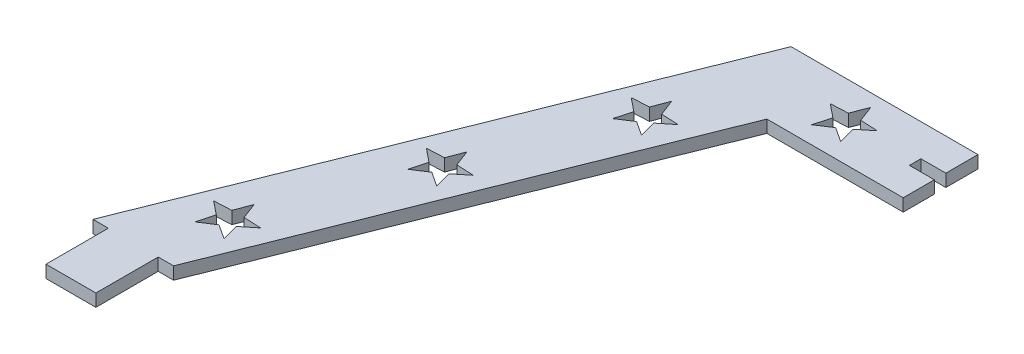
SolidWorks part; units mm, degrees
ref_plane "Front Plane" through (0, 0, 0) normal (0, 0, 1) x (1, 0, 0)
ref_plane "Top Plane" through (0, 0, 0) normal (0, 1, 0) x (1, 0, 0)
ref_plane "Right Plane" through (0, 0, 0) normal (1, 0, 0) x (0, 0, -1)
sketch "Sketch1" plane through (0, 0, 0) normal (0, 1, 0) x (1, 0, 0)
  line L0 (0, 0) -> (101.6, 0) construction
  line L1 (0, 0) -> (0, 127) construction
  line L2 (0, 127) -> (98.425, 127) construction
  line L3 (98.425, 127) -> (98.425, 118.8085)
  line L4 (98.425, 127) -> (50.8, 127)
  line L5 (50.8, 127) -> (0, 0)
  line L6 (0, 0) -> (3.9065, 0)
  line L7 (20.5175, 0) -> (63.6975, 107.95)
  line L8 (63.6975, 107.95) -> (98.425, 107.95)
  line L9 (3.9065, 0) -> (3.9065, -15.875)
  line L10 (3.9065, -15.875) -> (16.611, -15.875)
  line L11 (16.611, -15.875) -> (16.611, 0)
  line L12 (16.611, 0) -> (20.5175, 0)
  line L13 (98.425, 118.8085) -> (92.075, 118.8085)
  line L14 (92.075, 118.8085) -> (92.075, 115.8875)
  line L15 (92.075, 115.8875) -> (98.425, 115.8875)
  line L16 (98.425, 115.8875) -> (98.425, 107.95)
  line L17 (74.3563, 123.7542) -> (72.7878, 119.6338)
  line L18 (92.075, 117.348) -> (45.1512, 117.348) construction
  line L19 (50.8, 127) -> (63.6975, 107.95) construction
  line L20 (61.4274, 102.2747) -> (61.7931, 101.8616) construction
  line L21 (0, 0) -> (20.5175, 0) construction
  line L22 (10.2587, 0) -> (57.2487, 117.475) construction
  line L23 (80.3282, 119.4154) -> (75.9248, 119.6338)
  line L24 (74.3563, 123.7542) -> (75.9248, 119.6338)
  line L25 (80.3282, 119.4154) -> (76.8941, 116.6504)
  line L26 (78.0471, 112.395) -> (76.8941, 116.6504)
  line L27 (78.0471, 112.395) -> (74.3563, 114.8066)
  line L28 (70.6655, 112.395) -> (74.3563, 114.8066)
  line L29 (70.6655, 112.395) -> (71.8185, 116.6504)
  line L30 (68.3844, 119.4154) -> (71.8185, 116.6504)
  line L31 (68.3844, 119.4154) -> (72.7878, 119.6338)
  line L32 (47.6498, 99.7569) -> (46.0814, 95.6365)
  line L33 (53.6217, 95.4181) -> (49.2183, 95.6365)
  line L34 (47.6498, 99.7569) -> (49.2183, 95.6365)
  line L35 (53.6217, 95.4181) -> (50.1877, 92.6531)
  line L36 (51.3407, 88.3977) -> (50.1877, 92.6531)
  line L37 (51.3407, 88.3977) -> (47.6498, 90.8093)
  line L38 (43.959, 88.3977) -> (47.6498, 90.8093)
  line L39 (43.959, 88.3977) -> (45.112, 92.6531)
  line L40 (41.6779, 95.4181) -> (45.112, 92.6531)
  line L41 (41.6779, 95.4181) -> (46.0814, 95.6365)
  line L42 (32.7427, 62.489) -> (31.1742, 58.3686)
  line L43 (38.7146, 58.1502) -> (34.3111, 58.3686)
  line L44 (32.7427, 62.489) -> (34.3111, 58.3686)
  line L45 (38.7146, 58.1502) -> (35.2805, 55.3852)
  line L46 (36.4335, 51.1298) -> (35.2805, 55.3852)
  line L47 (36.4335, 51.1298) -> (32.7427, 53.5413)
  line L48 (29.0518, 51.1298) -> (32.7427, 53.5413)
  line L49 (29.0518, 51.1298) -> (30.2048, 55.3852)
  line L50 (26.7708, 58.1502) -> (30.2048, 55.3852)
  line L51 (26.7708, 58.1502) -> (31.1742, 58.3686)
  line L52 (17.2614, 23.7859) -> (15.693, 19.6655)
  line L53 (23.2333, 19.4471) -> (18.8299, 19.6655)
  line L54 (17.2614, 23.7859) -> (18.8299, 19.6655)
  line L55 (23.2333, 19.4471) -> (19.7993, 16.6821)
  line L56 (20.9523, 12.4267) -> (19.7993, 16.6821)
  line L57 (20.9523, 12.4267) -> (17.2614, 14.8383)
  line L58 (13.5706, 12.4267) -> (17.2614, 14.8383)
  line L59 (13.5706, 12.4267) -> (14.7236, 16.6821)
  line L60 (11.2895, 19.4471) -> (14.7236, 16.6821)
  line L61 (11.2895, 19.4471) -> (15.693, 19.6655)
  point P17 (98.425, 117.348)
  point P41 (74.3563, 117.475)
  point P43 (47.6498, 93.4777)
  point P54 (32.7427, 56.2098)
  point P66 (17.2614, 17.5067)
  dimension "D1" = 127
  dimension "D2" = 101.6
  dimension "D3" = 19.05
  dimension "D4" = 47.625
  dimension "D5" = 19.05
  dimension "D6" = 3.9065
  dimension "D7" = 3.9065
  dimension "D8" = 15.875
  dimension "D9" = 50.8
  dimension "D10" = 1.4605
  dimension "D11" = 1.4605
  dimension "D12" = 6.35
extrude "Boss-Extrude1" add sketch "Sketch1" against normal blind 3.175
